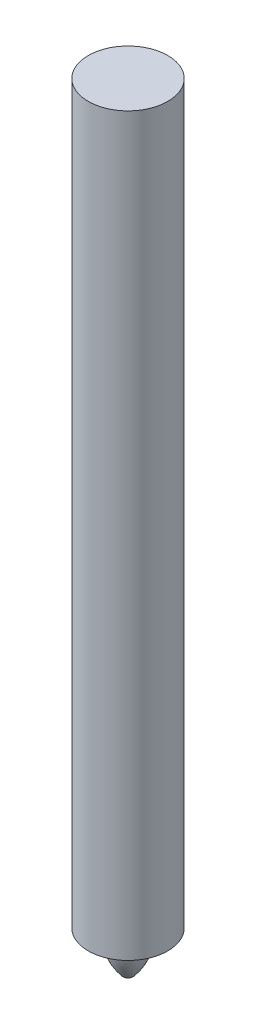
SolidWorks part; units mm, degrees
material "Rubber"
ref_plane "Front Plane" through (0, 0, 0) normal (0, 0, 1) x (1, 0, 0)
ref_plane "Top Plane" through (0, 0, 0) normal (0, 1, 0) x (1, 0, 0)
ref_plane "Right Plane" through (0, 0, 0) normal (1, 0, 0) x (0, 0, -1)
sketch "Sketch1" plane through (0, 0, 0) normal (0, 0, 1) x (1, 0, 0)
  line L0 (0, 0) -> (0, 123.825) construction
  line L1 (0, 123.825) -> (6.35, 123.825)
  line L2 (6.35, 123.825) -> (6.35, 6.35)
  line L3 (6.35, 6.35) -> (3.175, 6.35)
  line L5 (0.7937, 0) -> (0, 0)
  line L6 (0, 0) -> (0, 123.825)
  arc A0 (3.175, 6.35) -> (0.7937, 0) centre (-6.4823, 6.35) cw
  dimension "D1" = 6.35
  dimension "D2" = 0.7937
  dimension "D3" = 123.825
  dimension "D4" = 6.35
  dimension "D5" = 3.175
revolve "Revolve1" add sketch "Sketch1" angle 360 about L0
